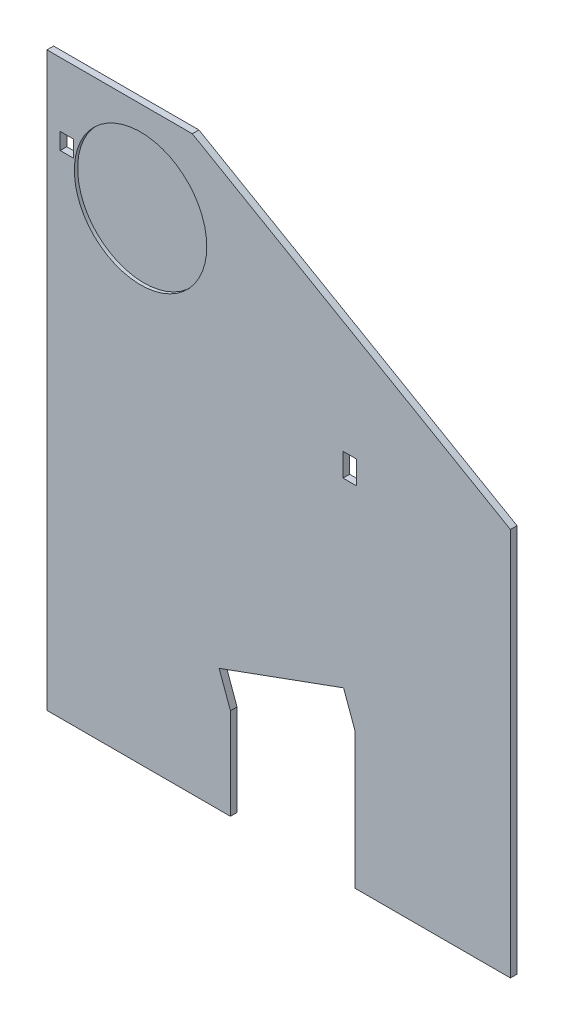
SolidWorks part; units mm, degrees
ref_plane "Front Plane" through (0, 0, 0) normal (0, 0, 1) x (1, 0, 0)
ref_plane "Top Plane" through (0, 0, 0) normal (0, 1, 0) x (1, 0, 0)
ref_plane "Right Plane" through (0, 0, 0) normal (1, 0, 0) x (0, 0, -1)
sketch "Sketch1" plane through (0, 0, 0) normal (0, 0, 1) x (1, 0, 0)
  line L19 (-70, 100) -> (-70, -72.7995) construction
  line L21 (70, -72.7995) -> (70, 44.5248) construction
  line L22 (-26.0859, 100) -> (70, 44.5248) construction
  line L23 (-26.0859, 100) -> (-70, 100) construction
  line L24 (-70, 100) -> (-70, -72.7995)
  line L25 (-70, -72.7995) -> (70, -72.7995)
  line L26 (70, -72.7995) -> (70, 44.5248)
  line L27 (-26.0859, 100) -> (70, 44.5248)
  line L28 (-26.0859, 100) -> (-70, 100)
extrude "Boss-Extrude1" add sketch "Sketch1" along normal blind 2
sketch "Sketch2" plane through (0, 0, 2) normal (0, 0, 1) x (1, 0, 0)
  line L5 (-26.0859, 100) -> (-70, 100)
  line L6 (-70, 100) -> (-70, -72.7995)
  line L7 (-70, -72.7995) -> (70, -72.7995)
  line L8 (70, -72.7995) -> (70, 44.5248)
  line L9 (70, 44.5248) -> (-26.0859, 100)
  line L10 (-26.0859, 100) -> (-70, 100)
  line L11 (-70, 100) -> (-70, -72.7995)
  line L12 (-70, -72.7995) -> (70, -72.7995)
  line L13 (70, -72.7995) -> (70, 44.5248)
  line L14 (70, 44.5248) -> (-26.0859, 100)
  circle A0 centre (-41.7237, 72.6554) radius 20
  dimension "D1" = 0
sketch "Sketch3" plane through (0, 0, 2) normal (0, 0, 1) x (1, 0, 0)
  line L0 (-17.9925, -35.7876) -> (19.5952, -22.1068)
  line L2 (19.5952, -22.1068) -> (23.0154, -31.5037)
  line L4 (-70, -65.3585) -> (-14.5723, -45.1845) construction
  line L5 (-66, 75.6554) -> (-62, 75.6554) construction
  line L6 (-66, 75.6554) -> (-62, 75.6554)
  line L7 (-66, 80.6554) -> (-66, 75.6554) construction
  line L8 (-66, 80.6554) -> (-62, 80.6554) construction
  line L9 (-62, 80.6554) -> (-62, 75.6554) construction
  line L10 (-26.0859, 100) -> (-70, 100)
  line L11 (-70, 100) -> (-70, -72.7995)
  line L12 (-70, -72.7995) -> (70, -72.7995)
  line L13 (70, -72.7995) -> (70, 44.5248)
  line L14 (70, 44.5248) -> (-26.0859, 100)
  line L15 (-26.0859, 100) -> (-70, 100)
  line L16 (-70, 100) -> (-70, -72.7995)
  line L17 (-70, -72.7995) -> (70, -72.7995)
  line L18 (70, -72.7995) -> (70, 44.5248)
  line L19 (70, 44.5248) -> (-26.0859, 100)
  line L20 (-66, 80.6554) -> (-66, 75.6554)
  line L21 (-66, 80.6554) -> (-62, 80.6554)
  line L22 (-62, 80.6554) -> (-62, 75.6554)
  line L23 (19.4272, 32.69) -> (23.4317, 32.69) construction
  line L24 (19.4272, 32.69) -> (19.4272, 39.6978) construction
  line L25 (23.4317, 32.69) -> (23.4317, 39.6978) construction
  line L26 (19.4272, 39.6978) -> (23.4317, 39.6978) construction
  line L27 (19.4272, 32.69) -> (23.4317, 32.69)
  line L28 (19.4272, 32.69) -> (19.4272, 39.6978)
  line L29 (23.4317, 32.69) -> (23.4317, 39.6978)
  line L30 (19.4272, 39.6978) -> (23.4317, 39.6978)
  line L31 (-17.9925, -35.7876) -> (-14.5723, -45.1845)
  line L32 (-14.5723, -45.1845) -> (-14.5723, -75.1845)
  line L33 (-14.5723, -75.1845) -> (23.0154, -75.1845)
  line L34 (23.0154, -75.1845) -> (23.0154, -31.5037)
  dimension "D1" = 10
  dimension "D2" = 30
  dimension "D3" = 0
extrude "Cut-Extrude1" cut sketch "Sketch3" against normal blind 10 contours L30 L28 L27 L29 | L22 L21 L20 L6 | L33 L34 L2 L0 L31 L32
sketch "Sketch4" plane through (0, 0, 2) normal (0, 0, 1) x (1, 0, 0)
  circle A0 centre (-41.7237, 72.6554) radius 20 construction
  circle A1 centre (-41.7237, 72.6554) radius 20
extrude "Cut-Extrude2" cut sketch "Sketch4" against normal blind 1
